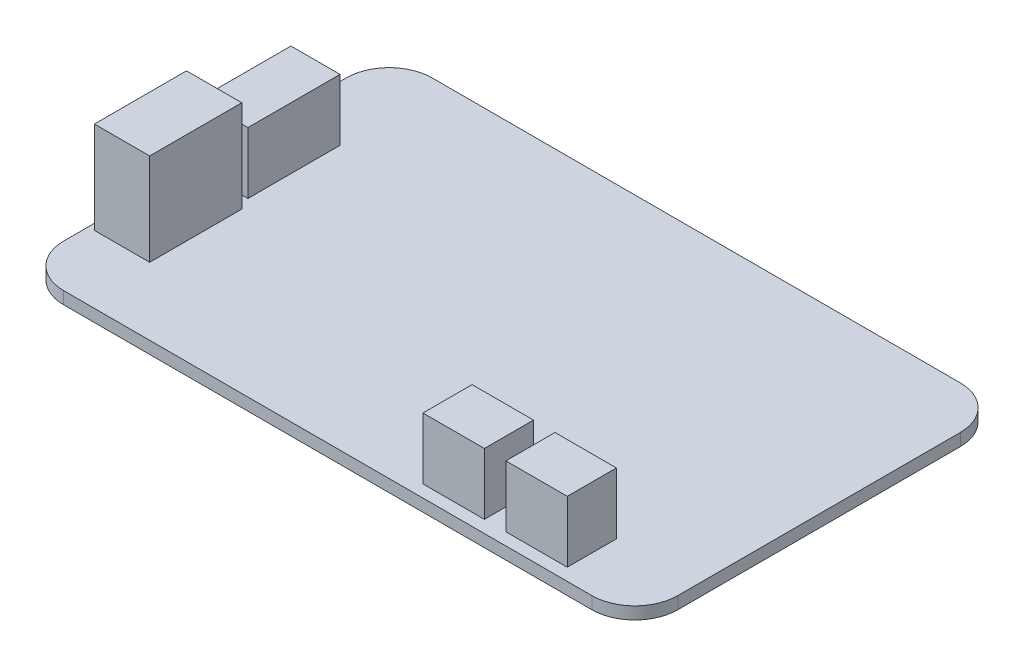
SolidWorks part; units mm, degrees
ref_plane "Front Plane" through (0, 0, 0) normal (0, 0, 1) x (1, 0, 0)
ref_plane "Top Plane" through (0, 0, 0) normal (0, 1, 0) x (1, 0, 0)
ref_plane "Right Plane" through (0, 0, 0) normal (1, 0, 0) x (0, 0, -1)
sketch "Sketch1" plane through (0, 0, 0) normal (0, 1, 0) x (1, 0, 0)
  line L1 (-50, 30) -> (50, 30)
  line L2 (-50, 30) -> (-50, -30)
  line L3 (-50, -30) -> (50, -30)
  line L4 (50, 30) -> (50, -30)
  line L5 (0, -30) -> (0, 30) construction
  line L6 (-50, 0) -> (50, 0) construction
  point P4 (0, 0)
  point P76 (0, 0)
  dimension "D1" = 60
  dimension "D2" = 100
extrude "Boss-Extrude1" add sketch "Sketch1" along normal blind 2
fillet "Fillet5" radius 7 1 edges at (50, 1, 30)
fillet "Fillet6" radius 7 1 edges at (50, 1, -30)
fillet "Fillet7" radius 7 1 edges at (-50, 1, -30)
fillet "Fillet8" radius 7 1 edges at (-50, 1, 30)
sketch "Sketch2" plane through (0, 2, 0) normal (0, 1, 0) x (1, 0, 0)
  line L0 (43, 30) -> (-43, 30) construction
  line L5 (-49, 13) -> (-41, 13)
  line L6 (-49, 13) -> (-49, -2)
  line L7 (-49, -2) -> (-41, -2)
  line L8 (-41, 13) -> (-41, -2)
  line L9 (-45, -2) -> (-45, 13) construction
  line L10 (-49, 5.5) -> (-41, 5.5) construction
  line L11 (-50, 23) -> (-50, -23) construction
  point P117 (-45, 5.5)
  dimension "D1" = 15
  dimension "D2" = 8
  dimension "D3" = 17
  dimension "D4" = 1
extrude "Boss-Extrude2" add sketch "Sketch2" along normal blind 10
sketch "Sketch3" plane through (0, 2, 0) normal (0, 1, 0) x (1, 0, 0)
  line L0 (-50, 23) -> (-50, -23) construction
  line L1 (-49, -4) -> (-40, -4)
  line L2 (-49, -4) -> (-49, -19)
  line L3 (-49, -19) -> (-40, -19)
  line L4 (-40, -4) -> (-40, -19)
  line L5 (-44.5, -19) -> (-44.5, -4) construction
  line L6 (-49, -11.5) -> (-40, -11.5) construction
  line L7 (-43, -30) -> (43, -30) construction
  point P72 (-44.5, -11.5)
  dimension "D1" = 15
  dimension "D2" = 9
  dimension "D3" = 1
  dimension "D4" = 11
extrude "Boss-Extrude3" add sketch "Sketch3" along normal blind 15
sketch "Sketch4" plane through (0, 2, 0) normal (0, 1, 0) x (1, 0, 0)
  line L0 (-43, -30) -> (43, -30) construction
  line L1 (27, -20) -> (37, -20)
  line L2 (27, -20) -> (27, -28)
  line L3 (27, -28) -> (37, -28)
  line L4 (37, -20) -> (37, -28)
  line L5 (32, -28) -> (32, -20) construction
  line L6 (27, -24) -> (37, -24) construction
  line L7 (50, -23) -> (50, 23) construction
  line L8 (27, -24) -> (23.5, -24) construction
  line L9 (25.25, -24) -> (25.25, -17.6354) construction
  line L10 (13.5, -20) -> (13.5, -28)
  line L11 (23.5, -28) -> (13.5, -28)
  line L12 (23.5, -20) -> (23.5, -28)
  line L13 (23.5, -20) -> (13.5, -20)
  point P10 (27, -24)
  point P72 (32, -24)
  dimension "D1" = 10
  dimension "D2" = 8
  dimension "D3" = 2
  dimension "D4" = 13
  dimension "D5" = 3.5
extrude "Boss-Extrude4" add sketch "Sketch4" along normal blind 10
